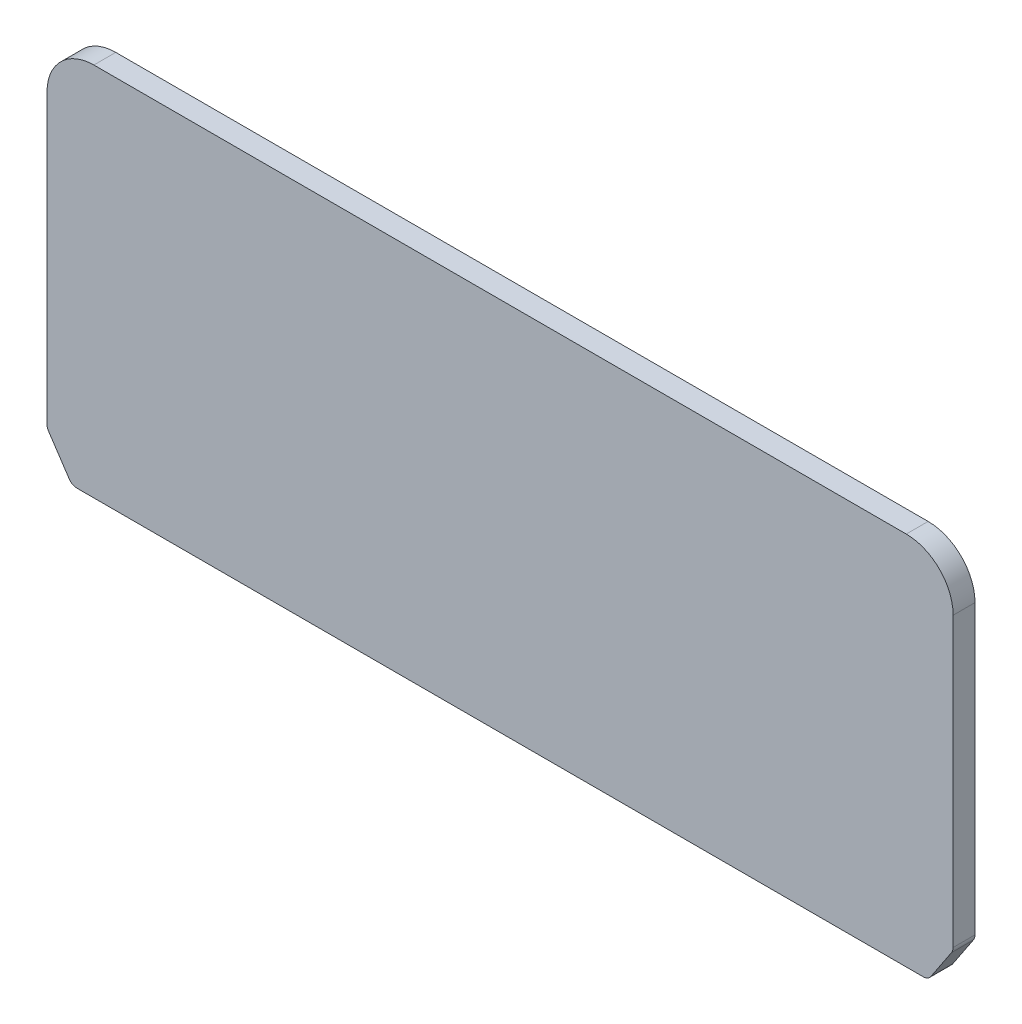
SolidWorks part; units mm, degrees
ref_plane "Plane1" through (0, 0, 0) normal (0, 0, 1) x (1, 0, 0)
ref_plane "Plane2" through (0, 0, 0) normal (0, 1, 0) x (1, 0, 0)
ref_plane "Plane3" through (0, 0, 0) normal (1, 0, 0) x (0, 0, -1)
sketch "Sketch1" plane through (0, 0, 0) normal (0, 0, 1) x (1, 0, 0)
  line L0 (-144.4962, 11.2442) -> (-137.8906, 1.3359)
  line L1 (-135.3944, 0) -> (135.3944, 0)
  line L2 (-145, 12.9083) -> (-145, 105)
  line L3 (-130, 120) -> (130, 120)
  line L4 (145, 12.9083) -> (145, 105)
  line L5 (0, 0) -> (0, 120) construction
  line L6 (144.4962, 11.2442) -> (137.8906, 1.3359)
  arc A0 (-145, 105) -> (-130, 120) centre (-130, 105) cw
  arc A1 (130, 120) -> (145, 105) centre (130, 105) cw
  arc A2 (137.8906, 1.3359) -> (135.3944, 0) centre (135.3944, 3) cw
  arc A3 (-137.8906, 1.3359) -> (-135.3944, 0) centre (-135.3944, 3) ccw
  arc A4 (-144.4962, 11.2442) -> (-145, 12.9083) centre (-142, 12.9083) cw
  arc A5 (144.4962, 11.2442) -> (145, 12.9083) centre (142, 12.9083) ccw
  point P14 (137, 0)
  point P17 (-137, 0)
  point P20 (-145, 12)
  point P23 (145, 12)
  dimension "D5" = 15
  dimension "D6" = 3
  dimension "D1" = 290
  dimension "D2" = 120
  dimension "D3" = 8
  dimension "D4" = 12
extrude "Extrude1" add sketch "Sketch1" along normal blind 7
